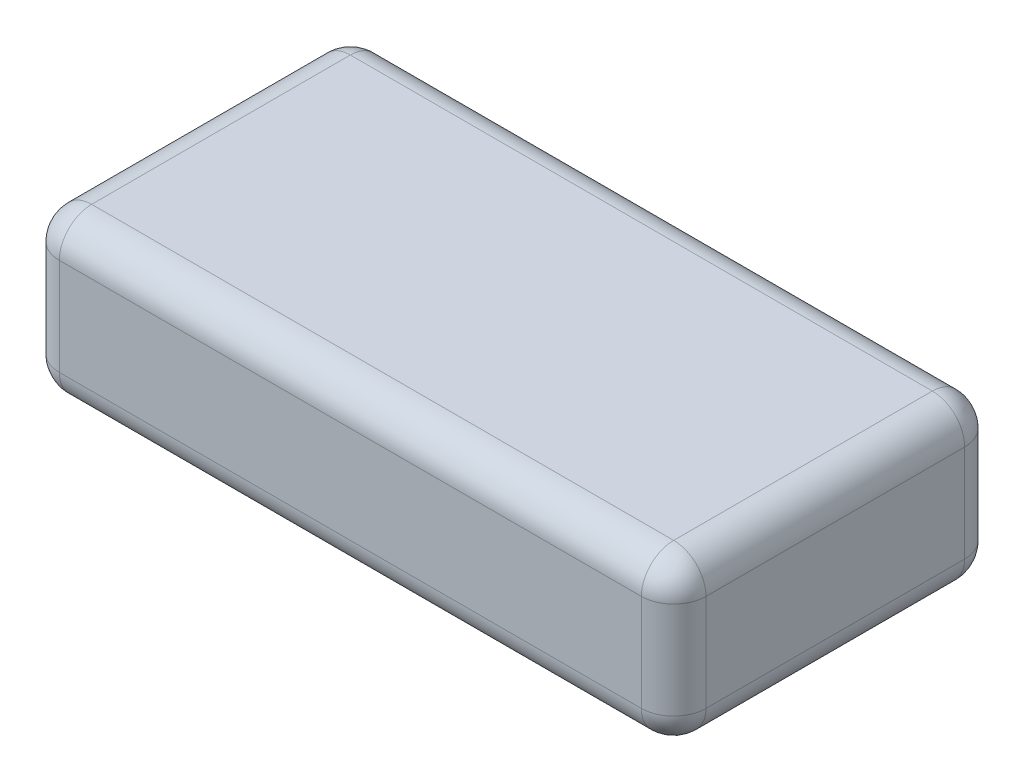
SolidWorks part; units mm, degrees
ref_plane "前视基准面" through (0, 0, 0) normal (0, 0, 1) x (1, 0, 0)
ref_plane "上视基准面" through (0, 0, 0) normal (0, 1, 0) x (1, 0, 0)
ref_plane "右视基准面" through (0, 0, 0) normal (1, 0, 0) x (0, 0, -1)
sketch "草图1" plane through (0, 0, 0) normal (0, 1, 0) x (1, 0, 0)
  line L1 (0, 0) -> (60, 0)
  line L2 (0, 0) -> (0, 30)
  line L3 (0, 30) -> (60, 30)
  line L4 (60, 0) -> (60, 30)
  dimension "D1" = 30
  dimension "D2" = 60
extrude "凸台-拉伸1" add sketch "草图1" along normal blind 15
fillet "圆角1" radius 3 12 edges at (30, 15, -30) (30, 0, -30) (30, 15, 0) (30, 0, 0) (0, 7.5, -30) (0, 15, -15) (0, 7.5, 0) (0, 0, -15) (60, 7.5, 0) (60, 15, -15) (60, 7.5, -30) (60, 0, -15)
